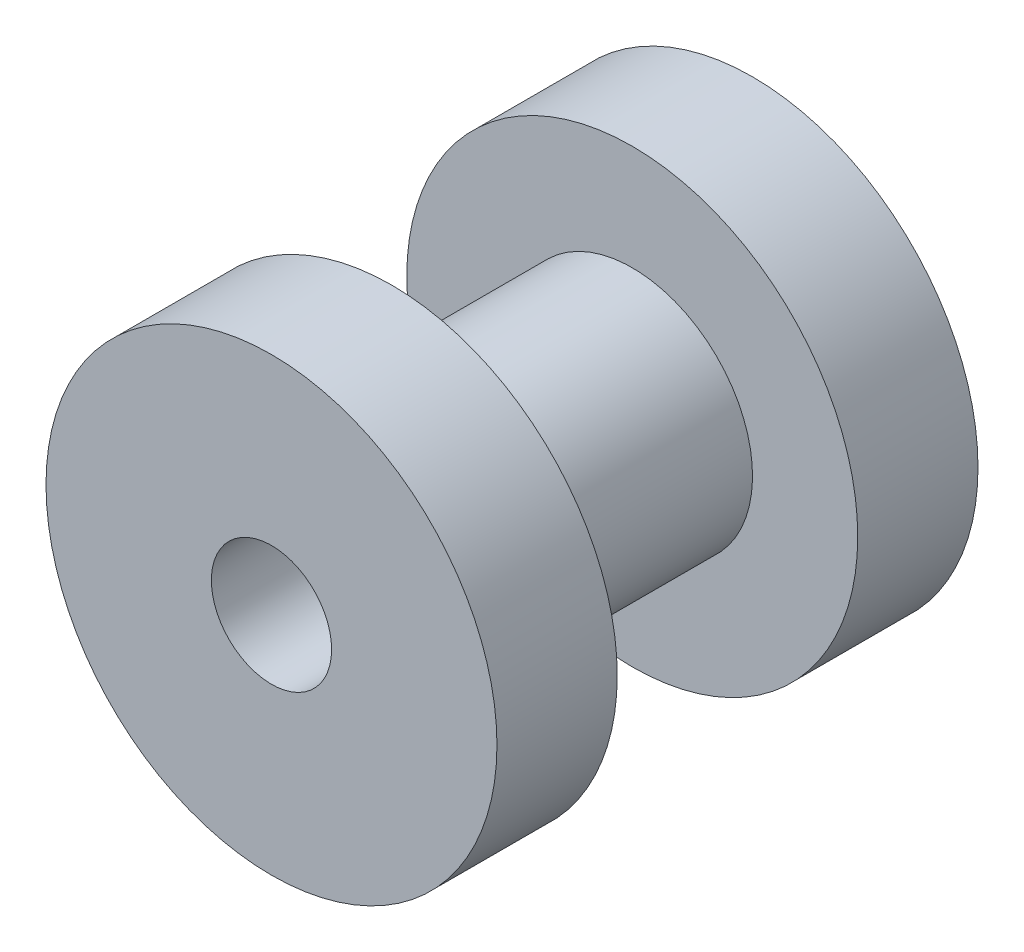
SolidWorks part; units mm, degrees
ref_plane "Front Plane" through (0, 0, 0) normal (0, 0, 1) x (1, 0, 0)
ref_plane "Top Plane" through (0, 0, 0) normal (0, 1, 0) x (1, 0, 0)
ref_plane "Right Plane" through (0, 0, 0) normal (1, 0, 0) x (0, 0, -1)
sketch "Sketch1" plane through (0, 0, 0) normal (0, 0, 1) x (1, 0, 0)
  circle A0 centre (0, 0) radius 4.7625
  dimension "D1" = 9.525
extrude "Boss-Extrude1" add sketch "Sketch1" along normal mid plane 10.16
sketch "Sketch2" plane through (0, 0, 0) normal (1, 0, 0) x (0, 0, -1)
  line L0 (0, 0) -> (5.08, 0) construction
  line L1 (5.08, -4.7625) -> (5.08, 4.7625) construction
  line L2 (5.08, 4.7625) -> (-5.08, 4.7625) construction
  line L3 (-2.54, 6.985) -> (2.54, 6.985)
  line L4 (-2.54, 6.985) -> (-2.54, 2.54)
  line L5 (-2.54, 2.54) -> (2.54, 2.54)
  line L6 (2.54, 6.985) -> (2.54, 2.54)
  line L7 (-2.54, 6.985) -> (2.54, 2.54) construction
  line L8 (-2.54, 2.54) -> (2.54, 6.985) construction
  point P5 (0, 4.7625)
  dimension "D1" = 5.08
  dimension "D2" = 2.54
revolve "Cut-Revolve1" cut sketch "Sketch2" angle 360 about L0
sketch "Sketch3" plane through (0, 0, 5.08) normal (0, 0, 1) x (1, 0, 0)
  circle A0 centre (0, 0) radius 1.27
  dimension "D1" = 2.54
extrude "Cut-Extrude1" cut sketch "Sketch3" against normal through all both and the other way through all
